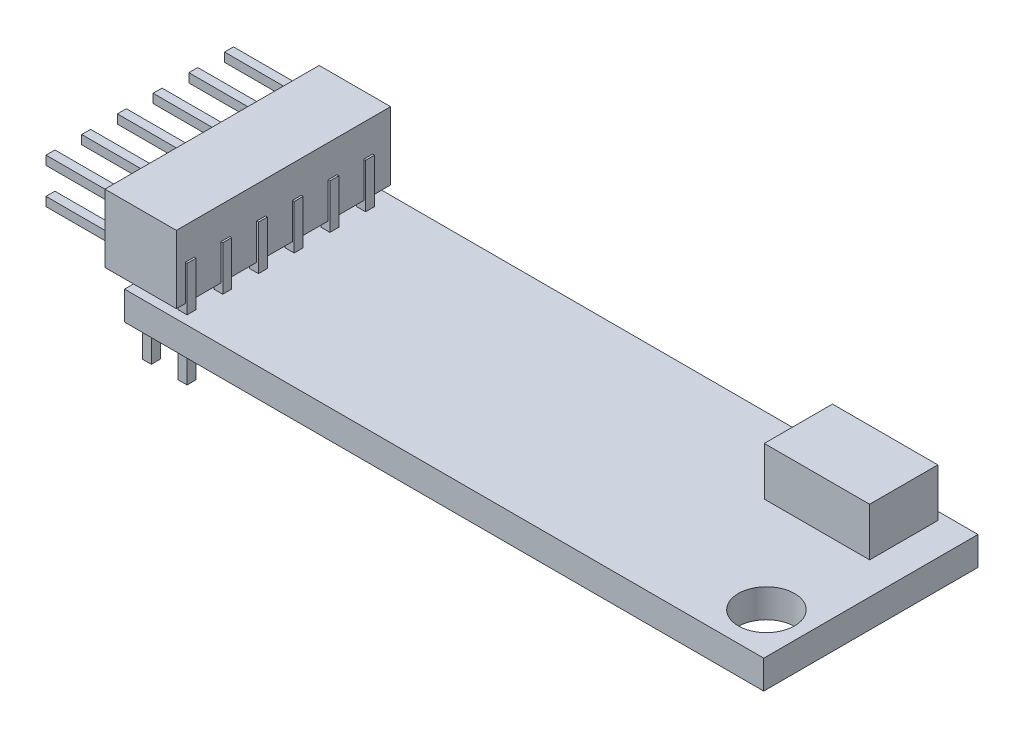
SolidWorks part; units mm, degrees
material "S-Glass Fiber"
ref_plane "Front Plane" through (0, 0, 0) normal (0, 0, 1) x (1, 0, 0)
ref_plane "Top Plane" through (0, 0, 0) normal (0, 1, 0) x (1, 0, 0)
ref_plane "Right Plane" through (0, 0, 0) normal (1, 0, 0) x (0, 0, -1)
sketch "Sketch1" plane through (0, 0, 0) normal (0, 1, 0) x (1, 0, 0)
  line L1 (-17.9, 6) -> (17.9, 6)
  line L2 (-17.9, 6) -> (-17.9, -6)
  line L3 (-17.9, -6) -> (17.9, -6)
  line L4 (17.9, 6) -> (17.9, -6)
  dimension "D1" = 12
  dimension "D2" = 6
  dimension "D3" = 35.8
  dimension "D4" = 17.9
extrude "Board" add sketch "Sketch1" along normal blind 1.6
sketch "Sketch2" plane through (0, 1.6, 0) normal (0, 1, 0) x (-1, 0, 0)
  line L1 (-17.9, 6) -> (-17.9, -6) construction
  line L4 (17.9, 6) -> (-17.9, 6) construction
  circle A0 centre (-15.625, 3.575) radius 1.575
  dimension "D1" = 3.15
  dimension "D2" = 0.7
  dimension "D3" = 0.85
extrude "Hole" cut sketch "Sketch2" against normal through all
sketch "Sketch3" plane through (0, 1.6, 0) normal (0, 1, 0) x (-1, 0, 0)
  line L0 (-17.9, -6) -> (17.9, -6) construction
  line L1 (-10.2, -5.55) -> (-16.1, -5.55)
  line L2 (-10.2, -5.55) -> (-10.2, -1.73)
  line L3 (-10.2, -1.73) -> (-16.1, -1.73)
  line L4 (-16.1, -5.55) -> (-16.1, -1.73)
  line L5 (-17.9, 6) -> (-17.9, -6) construction
  dimension "D1" = 5.9
  dimension "D2" = 3.82
  dimension "D3" = 0.45
  dimension "D4" = 1.8
extrude "Setup Switch" add sketch "Sketch3" along normal blind 2.7
sketch "Sketch4" plane through (0, 1.6, 0) normal (0, 1, 0) x (-1, 0, 0)
  line L0 (17.9, 6) -> (-17.9, 6) construction
  line L1 (17.4, 5.5) -> (16.9, 5.5)
  line L2 (17.4, 5.5) -> (17.4, 5)
  line L3 (17.4, 5) -> (16.9, 5)
  line L4 (16.9, 5.5) -> (16.9, 5)
  line L5 (17.9, -6) -> (17.9, 6) construction
  dimension "D1" = 0.5
  dimension "D2" = 0.5
  dimension "D3" = 0.5
  dimension "D4" = 0.5
extrude "Surface Connectors" add sketch "Sketch4" against normal blind 3.4 and the other way blind 2.5
pattern_linear "LPattern1" count 6 spacing 2 along (0, 0, -1) count 2 spacing 2 along (1, 0, 0) of "Surface Connectors"
sketch "Sketch5" plane through (0, 0, 6) normal (0, 0, 1) x (1, 0, 0)
  line L1 (-15, 2.1) -> (-19, 2.1)
  line L2 (-15, 2.1) -> (-15, 5.9)
  line L3 (-15, 5.9) -> (-19, 5.9)
  line L4 (-19, 2.1) -> (-19, 5.9)
  line L5 (-17.9, 1.6) -> (-17.9, 0) construction
  line L7 (-17.9, 1.6) -> (17.9, 1.6) construction
  dimension "D1" = 4
  dimension "D2" = 3.8
  dimension "D3" = 2.9
  dimension "D4" = 4.3
extrude "Connector Body" add sketch "Sketch5" against normal blind 12
sketch "Sketch6" plane through (-19, 0, 0) normal (-1, 0, 0) x (0, 0, 1)
  line L0 (6, 5.9) -> (6, 2.1) construction
  line L1 (5.5, 5.4) -> (5, 5.4)
  line L2 (5.5, 5.4) -> (5.5, 4.9)
  line L3 (5.5, 4.9) -> (5, 4.9)
  line L4 (5, 5.4) -> (5, 4.9)
  line L5 (-6, 5.9) -> (6, 5.9) construction
  dimension "D1" = 0.5
  dimension "D2" = 0.5
  dimension "D3" = 0.5
  dimension "D4" = 0.5
extrude "Connector Pin" add sketch "Sketch6" along normal blind 3.8
pattern_linear "LPattern2" count 6 spacing 2 along (0, 0, -1) count 2 spacing 2 along (0, -1, 0) of "Connector Pin"
